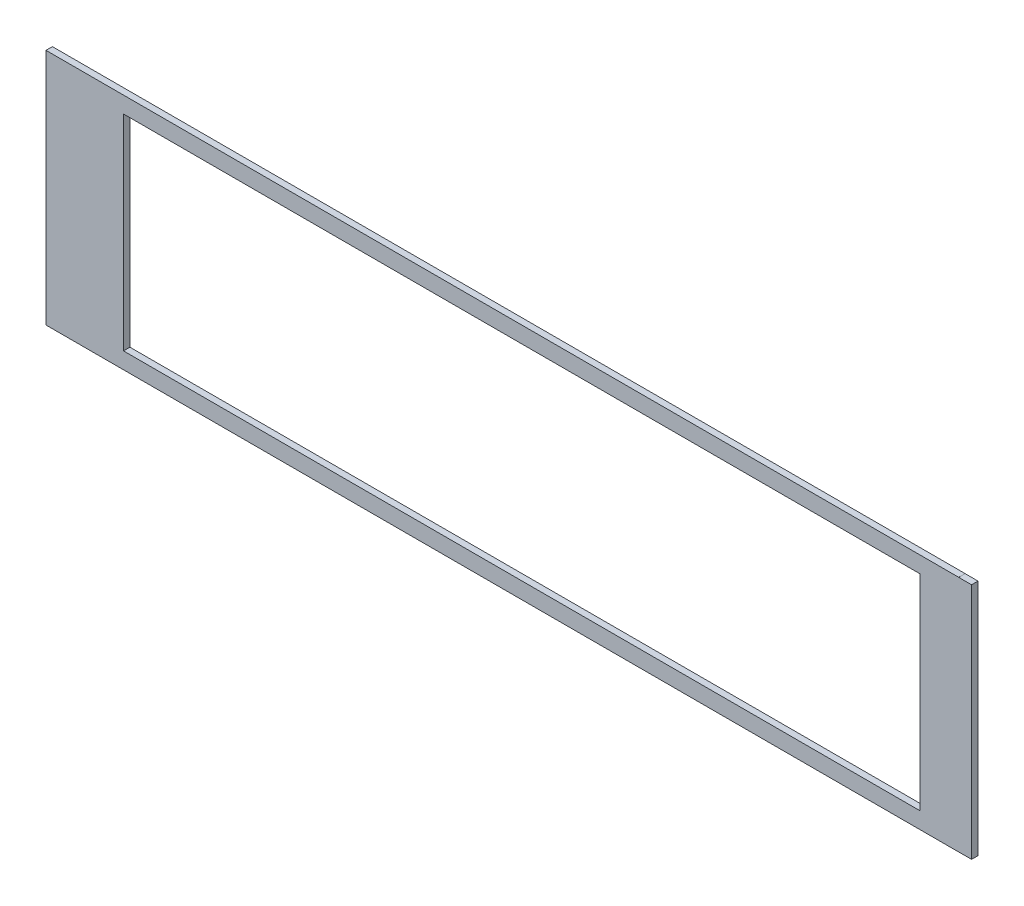
SolidWorks part; units mm, degrees
ref_plane "Front" through (0, 0, 0) normal (0, 0, 1) x (1, 0, 0)
ref_plane "Top" through (0, 0, 0) normal (0, 1, 0) x (1, 0, 0)
ref_plane "Right" through (0, 0, 0) normal (1, 0, 0) x (0, 0, -1)
sketch "Sketch1" plane through (0, 0, 0) normal (0, 0, 1) x (1, 0, 0)
  line L0 (222.3516, 58.7851) -> (-228.7016, 58.7851)
  line L1 (-228.7016, 58.7851) -> (-228.7016, -58.7851)
  line L2 (-228.7016, -58.7851) -> (222.3516, -58.7851)
  line L3 (222.3516, -58.7851) -> (222.3516, -58.7597)
  line L4 (222.3516, -58.7597) -> (228.7016, -58.7597)
  line L5 (228.7016, -58.7597) -> (228.7016, 58.7597)
  line L6 (228.7016, 58.7597) -> (222.3516, 58.7597)
  line L7 (222.3516, 58.7597) -> (222.3516, 58.7851)
  line L8 (-190.3984, 50.6984) -> (-190.3984, -50.6984)
  line L9 (-190.3984, -50.6984) -> (203.0984, -50.6984)
  line L10 (203.0984, -50.6984) -> (203.0984, 50.6984)
  line L11 (203.0984, 50.6984) -> (-190.3984, 50.6984)
extrude "Boss-Extrude1" add sketch "Sketch1" along normal blind 3.175
